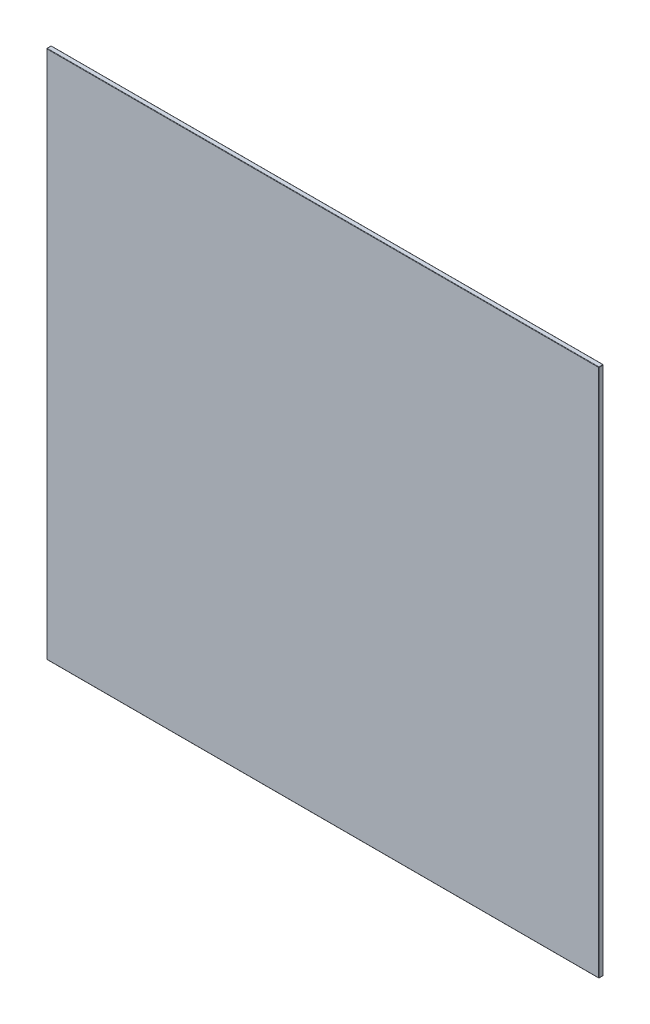
SolidWorks part; units mm, degrees
material "Glass"
ref_plane "Front Plane" through (0, 0, 0) normal (0, 0, 1) x (1, 0, 0)
ref_plane "Top Plane" through (0, 0, 0) normal (0, 1, 0) x (1, 0, 0)
ref_plane "Right Plane" through (0, 0, 0) normal (1, 0, 0) x (0, 0, -1)
sketch "Sketch1" plane through (0, 0, 0) normal (0, 0, 1) x (1, 0, 0)
  line L1 (-180, -172.5) -> (180, -172.5)
  line L2 (-180, -172.5) -> (-180, 172.5)
  line L3 (-180, 172.5) -> (180, 172.5)
  line L4 (180, -172.5) -> (180, 172.5)
  line L5 (-180, -172.5) -> (180, 172.5) construction
  line L6 (-180, 172.5) -> (180, -172.5) construction
  point P0 (0, 0)
  dimension "D1" = 345
  dimension "D2" = 360
extrude "Boss-Extrude1" add sketch "Sketch1" along normal blind 3
fillet "Fillet1" radius 0.25 12 edges at (0, 172.5, 3) (0, 172.5, 0) (180, 0, 3) (180, 172.5, 1.5) (180, 0, 0) (-180, 172.5, 1.5) (-180, 0, 3) (-180, 0, 0) (-180, -172.5, 1.5) (0, -172.5, 3) (180, -172.5, 1.5) (0, -172.5, 0)
